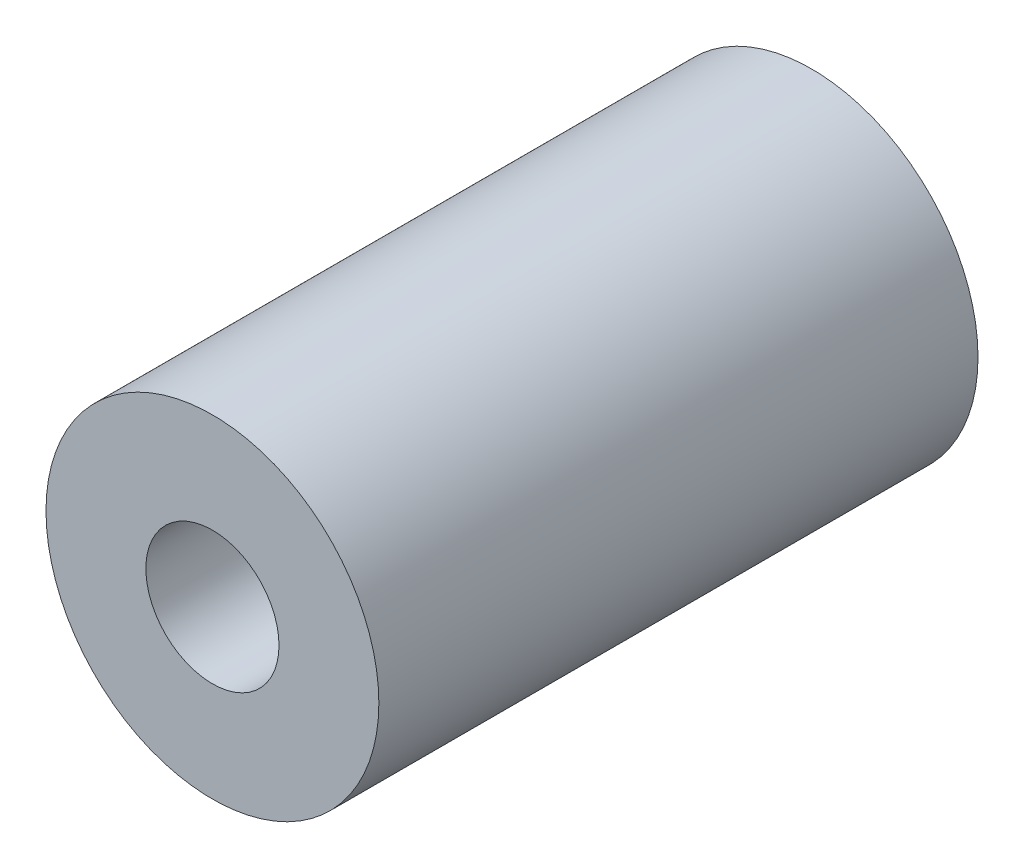
SolidWorks part; units mm, degrees
ref_plane "Front Plane" through (0, 0, 0) normal (0, 0, 1) x (1, 0, 0)
ref_plane "Top Plane" through (0, 0, 0) normal (0, 1, 0) x (1, 0, 0)
ref_plane "Right Plane" through (0, 0, 0) normal (1, 0, 0) x (0, 0, -1)
sketch "Sketch1" plane through (0, 0, 0) normal (0, 0, 1) x (1, 0, 0)
  circle A0 centre (0, 0) radius 15
  circle A1 centre (0, 0) radius 6
extrude "Boss-Extrude1" add sketch "Sketch1" along normal blind 54
